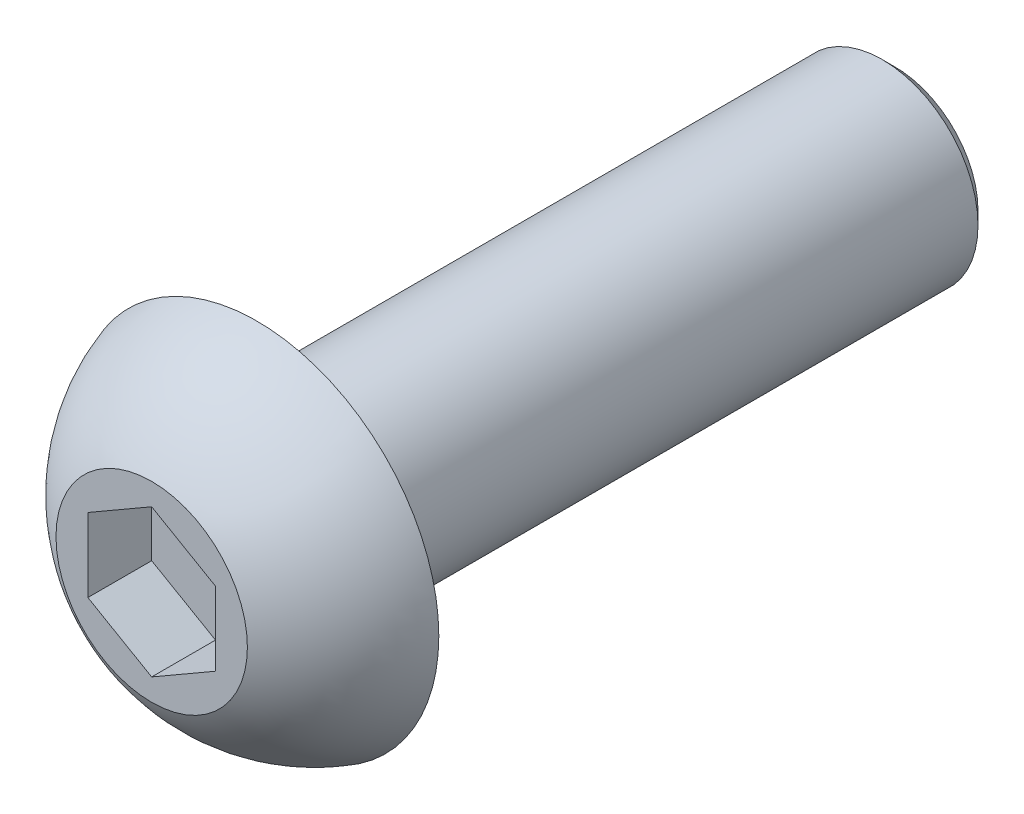
SolidWorks part; units mm, degrees
ref_plane "Front" through (0, 0, 0) normal (0, 0, 1) x (1, 0, 0)
ref_plane "Top" through (0, 0, 0) normal (0, 1, 0) x (1, 0, 0)
ref_plane "Right" through (0, 0, 0) normal (1, 0, 0) x (0, 0, -1)
sketch "Croquis1" plane through (0, 0, 0) normal (1, 0, 0) x (0, 0, -1)
  line L0 (0, 2.85) -> (0, 1.5)
  line L2 (0, 1.5) -> (10, 1.5)
  line L3 (10, 1.5) -> (10, 0)
  line L5 (10, 0) -> (-1.65, 0)
  line L7 (-1.65, 0) -> (-1.65, 1.5)
  line L9 (10, 0) -> (11.2578, 0) construction
  arc A1 (0, 2.85) -> (-1.65, 1.5) centre (0.8487, 0.1293) ccw
  dimension "D4" = 2.85
  dimension "D1" = 10
  dimension "D2" = 1.65
  dimension "D3" = 3
  dimension "D5" = 2.4987
  dimension "D6" = 5.7
revolve "Revolución1" add sketch "Croquis1" angle 360 about L9
sketch "Croquis2" plane through (0, 0, 1.65) normal (0, 0, 1) x (1, 0, 0)
  line L1 (0, 1.1547) -> (-1, 0.5774)
  line L2 (-1, 0.5774) -> (-1, -0.5774)
  line L3 (-1, -0.5774) -> (0, -1.1547)
  line L4 (0, -1.1547) -> (1, -0.5774)
  line L5 (1, -0.5774) -> (1, 0.5774)
  line L6 (1, 0.5774) -> (0, 1.1547)
  circle A0 centre (0, 0) radius 1 construction
  dimension "D1" = 2
extrude "Cortar-Extruir2" cut sketch "Croquis2" against normal blind 1
chamfer "Chaflán1" distance 0.2 angle 45 1 edges at (1.5, 0, -10)
